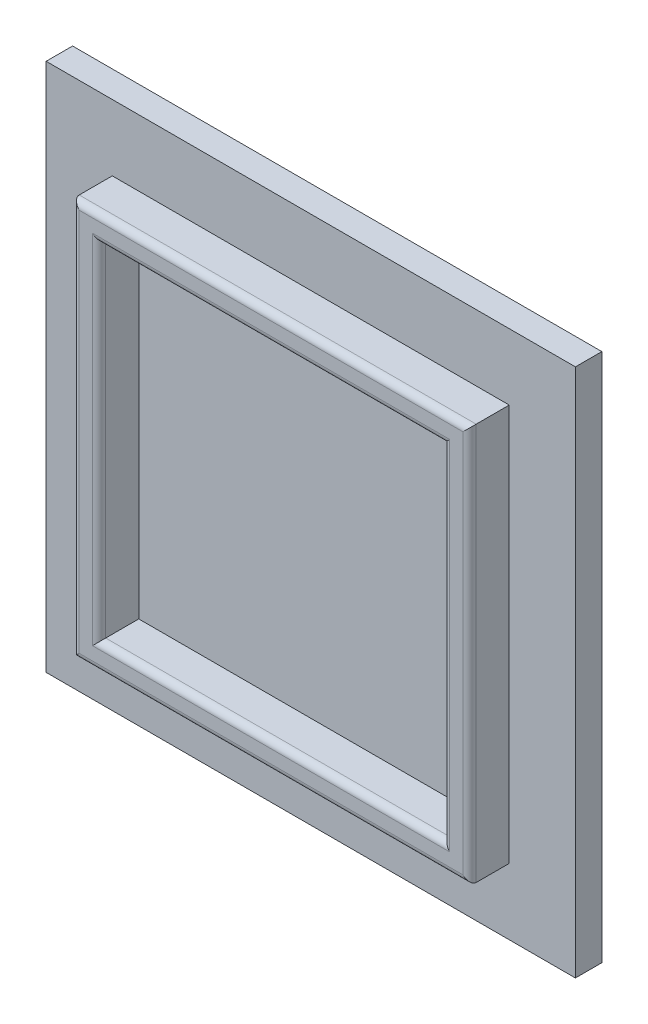
SolidWorks part; units mm, degrees
ref_plane "Front Plane" through (0, 0, 0) normal (0, 0, 1) x (1, 0, 0)
ref_plane "Top Plane" through (0, 0, 0) normal (0, 1, 0) x (1, 0, 0)
ref_plane "Right Plane" through (0, 0, 0) normal (1, 0, 0) x (0, 0, -1)
sketch "Sketch1" plane through (0, 0, 0) normal (0, 0, 1) x (1, 0, 0)
  line L1 (-25.1923, 15.1442) -> (14.8077, 15.1442)
  line L2 (-25.1923, 15.1442) -> (-25.1923, -24.8558)
  line L3 (-25.1923, -24.8558) -> (14.8077, -24.8558)
  line L4 (14.8077, 15.1442) -> (14.8077, -24.8558)
  dimension "D1" = 40
  dimension "D2" = 40
extrude "Boss-Extrude1" add sketch "Sketch1" along normal blind 2
sketch "Sketch2" plane through (0, 0, 2) normal (0, 0, 1) x (1, 0, 0)
  line L0 (-25.1923, 15.1442) -> (14.8077, -24.8558) construction
  line L1 (-25.1923, -24.8558) -> (14.8077, 15.1442) construction
  line L3 (9.8077, -19.8558) -> (-20.1923, -19.8558)
  line L4 (9.8077, -19.8558) -> (9.8077, 10.1442)
  line L5 (9.8077, 10.1442) -> (-20.1923, 10.1442)
  line L6 (-20.1923, -19.8558) -> (-20.1923, 10.1442)
  line L7 (9.8077, -19.8558) -> (-20.1923, 10.1442) construction
  line L8 (9.8077, 10.1442) -> (-20.1923, -19.8558) construction
  line L9 (7.8077, -17.8558) -> (-18.1923, -17.8558)
  line L10 (7.8077, -17.8558) -> (7.8077, 8.1442)
  line L11 (7.8077, 8.1442) -> (-18.1923, 8.1442)
  line L12 (-18.1923, -17.8558) -> (-18.1923, 8.1442)
  line L13 (7.8077, -17.8558) -> (-18.1923, 8.1442) construction
  line L14 (7.8077, 8.1442) -> (-18.1923, -17.8558) construction
  point P8 (-5.1923, -4.8558)
  point P9 (-5.1923, -4.8558)
  point P14 (-5.1923, -4.8558)
  dimension "D1" = 30
  dimension "D2" = 26
extrude "Boss-Extrude2" add sketch "Sketch2" along normal blind 3
fillet "Fillet2" radius 0.5 8 edges at (-5.1923, -19.8558, 5) (-5.1923, -17.8558, 5) (7.8077, -4.8558, 5) (9.8077, -4.8558, 5) (-18.1923, -4.8558, 5) (-5.1923, 8.1442, 5) (-5.1923, 10.1442, 5) (-20.1923, -4.8558, 5)
